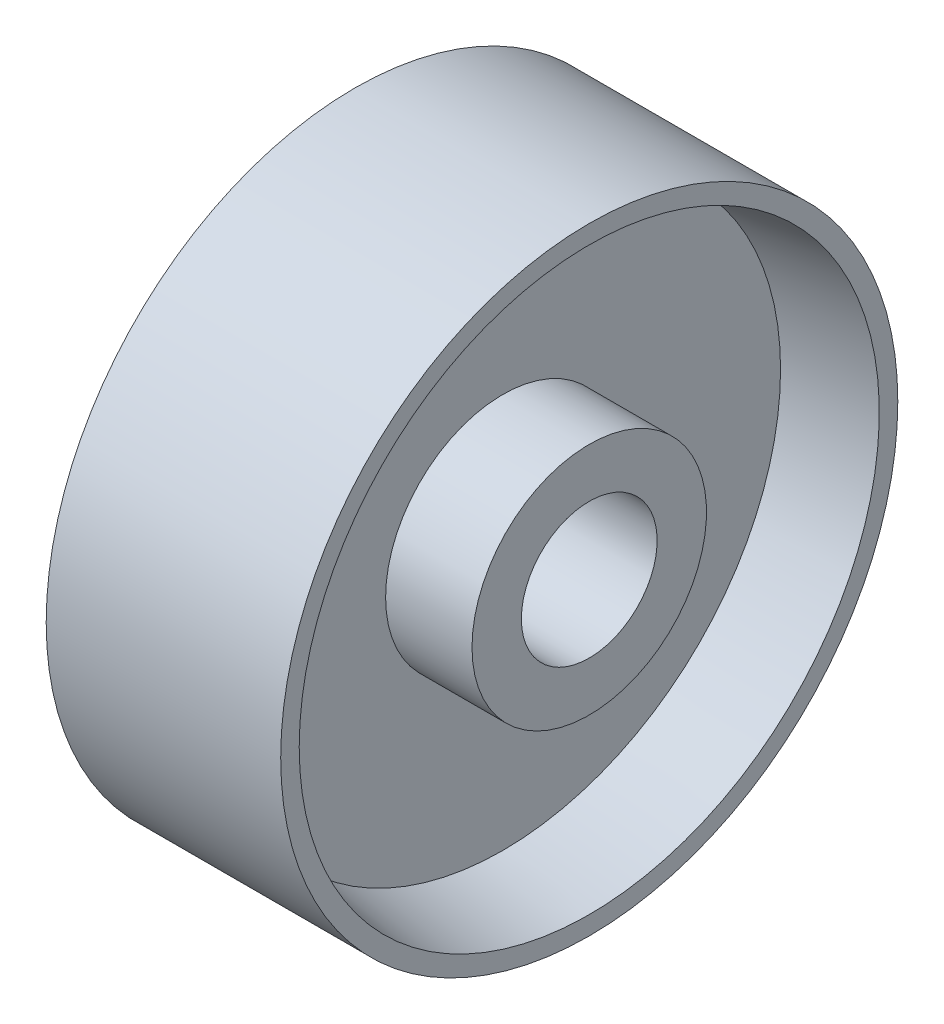
SolidWorks part; units mm, degrees
ref_plane "Alzado" through (0, 0, 0) normal (0, 0, 1) x (1, 0, 0)
ref_plane "Planta" through (0, 0, 0) normal (0, 1, 0) x (1, 0, 0)
ref_plane "Vista lateral" through (0, 0, 0) normal (1, 0, 0) x (0, 0, -1)
sketch "Croquis1" plane through (0, 0, 0) normal (0, 0, 1) x (1, 0, 0)
  line L0 (-14.7613, 0) -> (21.1484, 0) construction
  line L1 (19, 11) -> (-19, 11)
  line L2 (-19, 11) -> (-19, 19)
  line L3 (-19, 19) -> (-5, 19)
  line L4 (-5, 19) -> (-5, 45)
  line L5 (-5, 45) -> (-19, 47)
  line L6 (-19, 47) -> (-19, 50)
  line L7 (-19, 50) -> (19, 50)
  line L8 (19, 50) -> (19, 47)
  line L9 (19, 47) -> (5, 45)
  line L10 (5, 45) -> (5, 19)
  line L11 (5, 19) -> (19, 19)
  line L12 (19, 19) -> (19, 11)
  line L13 (0, 0) -> (0, 54.8888) construction
  point P17 (15.3876, 49.1095)
  point P18 (15.5164, 48.156)
  dimension "D1" = 11
  dimension "D2" = 38
  dimension "D3" = 19
  dimension "D4" = 50
  dimension "D5" = 10
  dimension "D6" = 5
  dimension "D7" = 3
  dimension "D8" = 38
revolve "Revolución1" add sketch "Croquis1" angle 360 about L0
